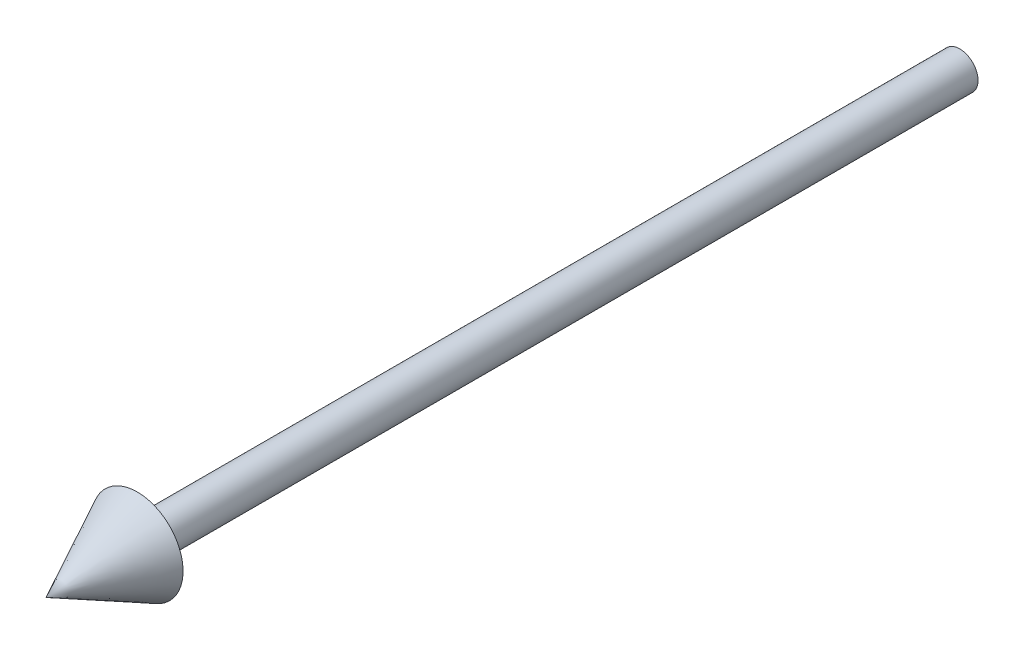
SolidWorks part; units mm, degrees
ref_plane "Front Plane" through (0, 0, 0) normal (0, 0, 1) x (1, 0, 0)
ref_plane "Top Plane" through (0, 0, 0) normal (0, 1, 0) x (1, 0, 0)
ref_plane "Right Plane" through (0, 0, 0) normal (1, 0, 0) x (0, 0, -1)
sketch "Sketch2" plane through (0, 0, 0) normal (0, 1, 0) x (1, 0, 0)
  line L0 (0, 41.95) -> (0, -114.4521) construction
  line L1 (-36.8894, 0) -> (41.4965, 0) construction
  line L2 (0, -100) -> (5, -90)
  line L3 (5, -90) -> (2, -90)
  line L4 (2, -90) -> (2, 0)
  line L5 (2, 0) -> (0, 0)
  line L6 (0, 0) -> (0, -100)
  dimension "D1" = 100
  dimension "D2" = 2
  dimension "D3" = 10
  dimension "D4" = 5
revolve "Revolve1" add sketch "Sketch2" angle 360 about L0
equation "\"frame_arrow_length\"=100"
equation "\"D1@Sketch2\"=\"frame_arrow_length\""
equation "\"frame_arrow_odA\"=4"
equation "\"D2@Sketch2\"=\"frame_arrow_odA\"/2"
equation "\"frame_arrow_head_od\"=5"
equation "\"D4@Sketch2\"=\"frame_arrow_head_od\""
equation "\"frame_arrow_head_length\"=10"
equation "\"D3@Sketch2\"=\"frame_arrow_head_length\""
equation "\"tvarobot_theta1\"=30"
equation "\"link0_ringA_odA\"= 40"
equation "\"link0_ringA_odB\"= 25"
equation "\"link0_ringA_id\"= 20"
equation "\"link0_ringA_thickness\"= (\"link0_ringA_odB\" - \"link0_ringA_id\")/2"
equation "\"link0_ringA_height\"= 3"
equation "\"link0_ringA_heightA\"= 1.5"
equation "\"link0_ringA_heightB\"=\"link0_ringA_height\"-\"link0_ringA_heightA\""
equation "\"link0_ringB_odA\"= 40"
equation "\"link0_ringB_odB\"= 29"
equation "\"link0_ringB_id\"= \"link0_shaftA_bearing_id\"+1"
equation "\"link0_ringB_thickness\"= (\"link0_ringB_odB\" - \"link0_ringB_id\")/2"
equation "\"link0_ringB_height\"= 3"
equation "\"link0_ringB_heightA\"= 1.5"
equation "\"link0_ringB_heightB\"=\"link0_ringB_height\"-\"link0_ringB_heightA\""
equation "\"link0_shaftA_bearing_od\"=27"
equation "\"link0_shaftA_bearing_id\"=20"
equation "\"link0_shaftA_thrust_bearing_od\"=35"
equation "\"link0_shaftA_thrust_bearing_id\"=20.04"
equation "\"link0_shaftA_retaining_ring_id\"=18.5"
equation "\"link0_shaftA_retaining_ring_groove_width\"=1.5"
equation "\"link0_shaftA_spline_length\"=8.0"
equation "\"link0_shaftA_spline_depth\"=1.0"
equation "\"link0_shaftA_spline_width\"=4.0"
equation "\"link0_shaftA_odA\"=\"link0_shaftA_bearing_id\""
equation "\"link0_shaftA_odB\"=35"
equation "\"link0_shaftA_odC\"=\"link0_shaftA_bearing_id\""
equation "\"link0_shaftA_odD\"=\"link0_shaftA_odC\"-2*\"link0_shaftA_spline_depth\""
equation "\"link0_shaftA_odE\"=\"link0_shaftA_bearing_id\""
equation "\"link0_shaftA_odF\"=\"link0_shaftA_odE\"-2*\"link0_shaftA_spline_depth\""
equation "\"link0_shaftA_idA\"=10"
equation "\"link0_shaftA_idB\"=6"
equation "\"link0_shaftA_length\"=39.5"
equation "\"link0_shaftA_lengthA\"=8.0"
equation "\"link0_shaftA_lengthB\"=12.0"
equation "\"link0_shaftA_lengthC\"=35.0"
equation "\"link0_shaftA_lengthD\"=39.0"
equation "\"link0_shaftA_lengthE\"=\"link0_shaftA_length\"-\"link0_shaftA_lengthD\""
equation "\"link0_shaftA_offsetX\"=11"
equation "\"link0_shaftA_offsetY\"=0"
equation "\"link0_shaftA_bolt_pattern_dia\"=14"
equation "\"link0_motor_center_dist\"=26"
equation "\"link0_46t_pulley_spline_length\"=8"
equation "\"link0_46t_pulley_spline_depth\"=\"link0_shaftA_spline_depth\"*1.025"
equation "\"link0_46t_pulley_spline_width\"=\"link0_shaftA_spline_width\"*1.05"
equation "\"link0_46t_pulley_idA\"=\"link0_shaftA_bearing_id\"*1.025"
equation "\"link0_46t_pulley_idB\"=\"link0_46t_pulley_idA\"-2*\"link0_46t_pulley_spline_depth\""
equation "\"link0_shaftB_spline_length\"=10"
equation "\"link0_shaftB_spline_depth\"=1.0"
equation "\"link0_shaftB_spline_width\"=1.25"
equation "\"link0_shaftB_length\"=7"
equation "\"link0_shaftB_lengthA\"=1.5"
equation "\"link0_shaftB_lengthB\"=2.75"
equation "\"link0_shaftB_odA\"=32"
equation "\"link0_shaftB_odB\"=22"
equation "\"link0_shaftB_odC\"=20"
equation "\"link0_shaftB_idA\"=10"
equation "\"link0_shaftB_bolt_diameter\"=19"
equation "\"link0_shaftB_bearing_od\"=27"
equation "\"link0_shaftB_bearing_id\"=20"
equation "\"link0_motor_length\"=46.5"
equation "\"link0_motor_width\"=28.5"
equation "\"link0_motor_height\"=34"
equation "\"link0_motor_offset\"=8"
equation "\"link0_shellA_thickness\"=2.5"
equation "\"link0_shellB_thickness\"=\"link0_shellA_thickness\""
equation "\"link0_plateA_shellA_height\"=48"
equation "\"link0_shellA_width\" =\"link0_plateA_width\""
equation "\"link0_shellA_height\" = \"link0_plateA_shellA_height\"-\"link0_plateA_height\""
equation "\"link0_shellA_length\" = \"link0_plateA_lengthB\" "
equation "\"link0_shellB_length\"=\"link0_shellA_length\""
equation "\"link0_shellA_radius\" = 0.375*25.4"
equation "\"link0_shellA_radiusA\"= \"link0_plateA_radiusA\""
equation "\"link0_shellA_radiusB\"= \"link0_plateA_radiusB\""
equation "\"link0_shellA_radiusC\"= 3"
equation "\"link0_postA_height\"=7"
equation "\"link0_postA_width\"=16"
equation "\"link0_postA_length\"=20"
equation "\"link0_postA_posX\"=22"
equation "\"link0_postA_posY\"=17.5"
equation "\"link0_postA_pocket_width\"=6.0"
equation "\"link0_postA_pocket_length\"=2.5"
equation "\"link0_postA_pocket_depth\"=9"
equation "\"link0_postA_pocket_posZ\"=10"
equation "\"link0_postB_height\"=7"
equation "\"link0_postB_width\"=16"
equation "\"link0_postB_length\"=20"
equation "\"link0_postB_posX\"=22"
equation "\"link0_postB_posY\"=17.5"
equation "\"link0_postB_id\"=3.0"
equation "\"link0_postB_pocket_width\"=6.0"
equation "\"link0_postB_pocket_length\"=2.5"
equation "\"link0_postB_pocket_depth\"=9"
equation "\"link0_postB_pocket_posZ\"=10"
equation "\"link0_postC_height\"=7"
equation "\"link0_postC_width\"=16"
equation "\"link0_postC_length\"=20"
equation "\"link0_postC_posX\"=22"
equation "\"link0_postC_posY\"=17.5"
equation "\"link0_postC_id\"=3.0"
equation "\"link0_postC_pocket_width\"=6.0"
equation "\"link0_postC_pocket_length\"=2.5"
equation "\"link0_postC_pocket_depth\"=9"
equation "\"link0_postC_pocket_posZ\"=10"
equation "\"link0_postD_height\"=7"
equation "\"link0_postD_width\"=16"
equation "\"link0_postD_length\"=20"
equation "\"link0_postD_posX\"=22"
equation "\"link0_postD_posY\"=17.5"
equation "\"link0_postD_id\"=3.0"
equation "\"link0_postD_pocket_width\"=6.0"
equation "\"link0_postD_pocket_length\"=3.0"
equation "\"link0_postD_pocket_depth\"=9"
equation "\"link0_postD_pocket_posZ\"=10"
equation "\"link0_postE_height\"=5"
equation "\"link0_postE_width\"=16"
equation "\"link0_postE_length\"=\"link0_plateE_lengthA\"-\"link0_lip_height\""
equation "\"link0_postE_posZ\"=22"
equation "\"link0_postE_posX\"=17.5"
equation "\"link0_postE_posY\"=22"
equation "\"link0_postE_id\"=3.0"
equation "\"link0_postE_cbore_id\"=6.5"
equation "\"link0_postE_hole_id\"=3"
equation "\"link0_postF_posZ\"=22"
equation "\"link0_postF_posX\"=17.5"
equation "\"link0_postF_posY\"=\"link0_plateB_lengthA\"+4"
equation "\"link0_postF_id\"=3.0"
equation "\"link0_postF_cbore_id\"=6.5"
equation "\"link0_postF_hole_id\"=3"
equation "\"link0_postG_posZ\"=22"
equation "\"link0_postG_posX\"=17.5"
equation "\"link0_postG_posY\"=\"link0_plateB_lengthA\"+12"
equation "\"link0_postG_id\"=3.0"
equation "\"link0_postG_cbore_id\"=6.5"
equation "\"link0_postG_hole_id\"=3"
equation "\"link0_postHIJ_posY\"=6"
equation "\"link0_postH_posX\"=28"
equation "\"link0_postH_posY\"=20"
equation "\"link0_postH_posZ\"=20"
equation "\"link0_postH_length\"=10"
equation "\"link0_postI_posX\"=28"
equation "\"link0_postI_posY\"=20"
equation "\"link0_postI_posZ\"=135"
equation "\"link0_postI_length\"=10"
equation "\"link0_postJ_posX\"=28"
equation "\"link0_postJ_posY\"=20"
equation "\"link0_postJ_posZ\"=175"
equation "\"link0_postJ_length\"=10"
equation "\"link0_postK_posX\"=28"
equation "\"link0_postK_posY\"=20"
equation "\"link0_postK_posZ\"=175"
equation "\"link0_postK_length\"=10"
equation "\"link0_postL_posX\"=28"
equation "\"link0_postL_posY\"=20"
equation "\"link0_postL_posZ\"=135"
equation "\"link0_postL_length\"=10"
equation "\"link0_postM_posX\"=28"
equation "\"link0_postM_posY\"=20"
equation "\"link0_postM_posZ\"=35"
equation "\"link0_postM_length\"=10"
equation "\"link0_plateA_lengthA\"=30"
equation "\"link0_plateA_lengthB\"=150"
equation "\"link0_plateA_lengthC\"=30"
equation "\"link0_plateA_length\"=\"link0_plateA_lengthA\"+\"link0_plateA_lengthB\"+\"link0_plateA_lengthC\""
equation "\"link0_plateA_width\"=  68"
equation "\"link0_plateA_height\"= \"link0_plateA_radiusA\""
equation "\"link0_plateA_thickness\"=\"link0_shellA_thickness\""
equation "\"link0_plateA_radius\"= 9.5"
equation "\"link0_plateA_radiusA\"= 18"
equation "\"link0_plateA_radiusB\"= 18"
equation "\"link0_plateA_radiusC\"= 3"
equation "\"link0_plateB_length\"= 40"
equation "\"link0_plateB_width\"= \"link0_plateA_width\"*1.005"
equation "\"link0_plateB_height\"= \"link0_plateA_shellA_height\"*1.005"
equation "\"link0_plateB_lengthA\"=\"link0_lip_height\"+\"link0_plateD_thickness\"+\"link0_motor_mount_thickness\""
equation "\"link0_plateB_lengthB\"=\"link0_plateB_height\"-\"link0_plateB_lengthA\""
equation "\"link0_plateB_radiusA\"= \"link0_plateA_radiusA\""
equation "\"link0_plateB_radiusB\"= \"link0_plateA_radiusB\""
equation "\"link0_plateB_radiusC\"= 3"
equation "\"link0_plateB_idA\"=\"link0_shaftA_odC\"+1"
equation "\"link0_plateB_idB\"=\"link0_shaftA_bearing_od\"-2"
equation "\"link0_plateB_idC\"=\"link0_shaftA_bearing_od\"*1.005"
equation "\"link0_plateB_idD\"=\"link0_shaftA_thrust_bearing_od\"+1 "
equation "\"link0_plateB_depthA\"=1.0"
equation "\"link0_plateB_depthB\"=2.0"
equation "\"link0_plateB_depthC\"=8"
equation "\"link0_plateB_depthD\"=\"link0_plateB_length\"-\"link0_lip_height\"-\"link0_plateD_thickness\" "
equation "\"link0_plateC_length\"=\"link0_plateB_length\""
equation "\"link0_plateC_width\"= \"link0_plateB_width\""
equation "\"link0_plateC_height\"= .1*25.4"
equation "\"link0_plateA_hole_od\" = 0.1*25.4"
equation "\"link0_plateA_hole_delx\" = 0.5*25.4"
equation "\"link0_plateA_hole_delz\" = 0.75*25.4"
equation "\"link0_plateA_hole_offx\" = 0.0*25.4"
equation "\"link0_plateA_hole_offz\" = \"link0_plateA_length\"/2"
equation "\"link0_plateB_hole_od\" = 0.1*25.4"
equation "\"link0_plateB_hole_delx\"= 0.75*25.4"
equation "\"link0_plateB_hole_delz\"= 0.75*25.4"
equation "\"link0_plateB_hole_offx\"= 0.0*25.4"
equation "\"link0_plateB_hole_offz\"= 0.0*25.4"
equation "\"link0_plateC_hole_od\"= 0.1*25.4"
equation "\"link0_plateC_hole_delx\"= 0.75*25.4"
equation "\"link0_plateC_hole_delz\"= 0.75*25.4"
equation "\"link0_plateC_hole_offx\"= 0.0*25.4"
equation "\"link0_plateC_hole_offz\"= 0.0*25.4"
equation "\"link0_plateD_height\"=\"link0_plateB_height\"-2*\"link0_shellA_thickness\""
equation "\"link0_plateD_width\"=\"link0_plateB_width\"-2*\"link0_shellA_thickness\""
equation "\"link0_plateD_thickness\"=10"
equation "\"link0_plateD_radiusA\"=\"link0_plateB_radiusA\"-\"link0_shellA_thickness\""
equation "\"link0_plateD_odA\"= .375*25.4"
equation "\"link0_plateD_odB\"= .375*25.4"
equation "\"link0_plateD_bearing_id\"=20"
equation "\"link0_plateD_bearing_od\"=27"
equation "\"link0_plateE_radiusA\"=\"link0_plateA_radiusA\""
equation "\"link0_plateE_radiusB\"=\"link0_plateA_radiusB\""
equation "\"link0_plateE_radiusC\"=8.0"
equation "\"link0_plateE_length\"=30"
equation "\"link0_plateE_lengthA\"=16"
equation "\"link0_plateE_height\"=\"link0_plateB_height\""
equation "\"link0_plateE_width\"=\"link0_plateB_width\""
equation "\"link0_plateE_odA\"=\"gantry_coupler_id\"*0.99"
equation "\"link0_plateE_idA\"=\"link0_plateE_odA\"-20.0"
equation "\"link0_plateE_spline_depth\"=\"link0_poleA_spline_depth\"*1.05"
equation "\"link0_plateE_spline_width\"=\"link0_poleA_spline_width\"*1.075"
equation "\"link0_plateE_spline_length\"=\"link0_poleA_spline_length\""
equation "\"link0_plateE_coupler_length\"=46"
equation "\"link0_lip_height\"=5.0"
equation "\"link0_lip_thickness\"=2.0"
equation "\"link0_motor_mount_thickness\"=8.0"
equation "\"link0_motor_mount_idA\"=22"
equation "\"link0_motor_mount_idB\"=\"link0_shaftB_bearing_od\"*1.005"
equation "\"link0_motor_mount_idC\"=\"link0_shaftB_bearing_od\"-2"
equation "\"link0_motor_mount_depthA\"=5.5"
equation "\"link0_motor_mount_height\"=\"link0_plateD_height\""
equation "\"link0_motor_mount_width\"=\"link0_plateD_width\""
equation "\"link0_motor_mountL_height\"=36"
equation "\"link0_motor_mountL_heightA\"=12"
equation "\"link0_motor_mountL_length\"=50"
equation "\"link0_motor_mountL_lengthA\"=36"
equation "\"gantry_coupler_od\"=25.4*2.0"
equation "\"gantry_coupler_id\"=1.645*25.4"
equation "\"gantry_coupler_offsetX\"=\"link0_plateE_width\"/2"
equation "\"link0_poleA_odA\"=20"
equation "\"link0_poleA_odB\"=36"
equation "\"link0_poleA_idA\"=\"link0_poleA_odA\"-2*\"link0_poleA_thickness\""
equation "\"link0_poleA_idB\"=(\"link0_plateE_idA\"/2+1.5*\"link0_lip_thickness\")*1.04"
equation "\"link0_poleA_thickness\"=3.5"
equation "\"link0_poleA_length\"=100"
equation "\"link0_poleA_lengthA\"=18.5"
equation "\"link0_poleA_lengthB\"=80"
equation "\"link0_poleA_gasket_thickness\"=1.5"
equation "\"link0_poleA_spline_depth\"=1.0"
equation "\"link0_poleA_spline_width\"=4.0"
equation "\"link0_poleA_spline_length\"=10.0"
equation "\"link1_plateB_length\"=30"
equation "\"link1_lip_height\"=\"link0_lip_height\""
equation "\"link0_tension_plateA_width\"=12"
equation "\"link0_tension_plateA_lengthA\"=10.5"
equation "\"link0_tension_plateB_width\"=\"link0_tension_plateA_width\""
equation "\"link0_tension_plateB_lengthA\"=\"link0_tension_plateA_lengthA\""
equation "\"link0_tension_wheelA_posZ\"=7"
equation "\"link0_tension_wheelA_posX\"=\"link0_plateD_height\"/2-\"link0_tension_plateA_lengthA\""
equation "\"link0_m2_clear_hole_id\"=2.35"
equation "\"link0_m2_insert_hole_id\"=2.5"
equation "\"link0_m2_tap_hole_id\"=1.75"
equation "\"link0_m2_nut_socket_width\"=4.25"
equation "\"link0_m2_nut_socket_depth\"=2.5"
equation "\"link0_m2_cbore_id\"=3.75"
equation "\"link0_m2_cbore_depth\"=7"
equation "\"link0_m2_5_clear_hole_id\"=2.75"
equation "\"link0_m2_5_insert_hole_id\"=2.75"
equation "\"link0_m2_5_tap_hole_id\"=2.25"
equation "\"link0_m2_5_nut_socket_width\"=5.25"
equation "\"link0_m2_5_nut_socket_depth\"=2.5"
equation "\"link0_m2_5_cbore_id\"=4.75"
equation "\"link0_m2_5_cbore_depth\"=2.5"
equation "\"link0_m2_5_insert_access_length\"=6.0"
equation "\"link0_m2_5_insert_access_width\"=3.0"
equation "\"link0_m3_clear_hole_id\"=3.25"
equation "\"link0_m3_insert_hole_id\"=3"
equation "\"link0_m3_tap_hole_id\"=2.75"
equation "\"link0_m3_nut_socket_width\"=5.75"
equation "\"link0_m3_nut_socket_depth\"=4.0"
equation "\"link0_m3_cbore_id\"=5.75"
equation "\"link0_m3_cbore_depth\"=3.5"
equation "\"link0_m3_insert_access_length\"=4.5"
equation "\"link0_m3_insert_access_width\"=3.5"
equation "\"link0_rpi_mount_height\"=6"
equation "\"link0_rpi_mount_width\"=49"
equation "\"link0_rpi_mount_length\"=58"
equation "\"link0_rpi_mount_post_od\"=6"
equation "\"link0_rpi_mount_posZ\"=72"
equation "\"link0_rpi_mount_posX\"=11.5"
equation "\"link0_mcu_mount_height\"=5"
equation "\"link0_mcu_mount_width\"=49"
equation "\"link0_mcu_mount_length\"=58"
equation "\"link0_mcu_mount_post_od\"=6"
equation "\"link0_mcu_mount_posZ\"=164"
equation "\"link0_mcu_mount_posX\"=4"
equation "\"link0_pwr_mount_height\"=4"
equation "\"link0_pwr_mount_width\"=15.75"
equation "\"link0_pwr_mount_length\"=75.75"
equation "\"link0_pwr_mount_post_od\"=6"
equation "\"link0_pwr_mount_posZ\"=75"
equation "\"link0_pwr_mount_posX\"=16"
equation "\"link0_pwr_board_height\"=6"
equation "\"link0_pwr_board_width\"=21"
equation "\"link0_pwr_board_length\"=80"
